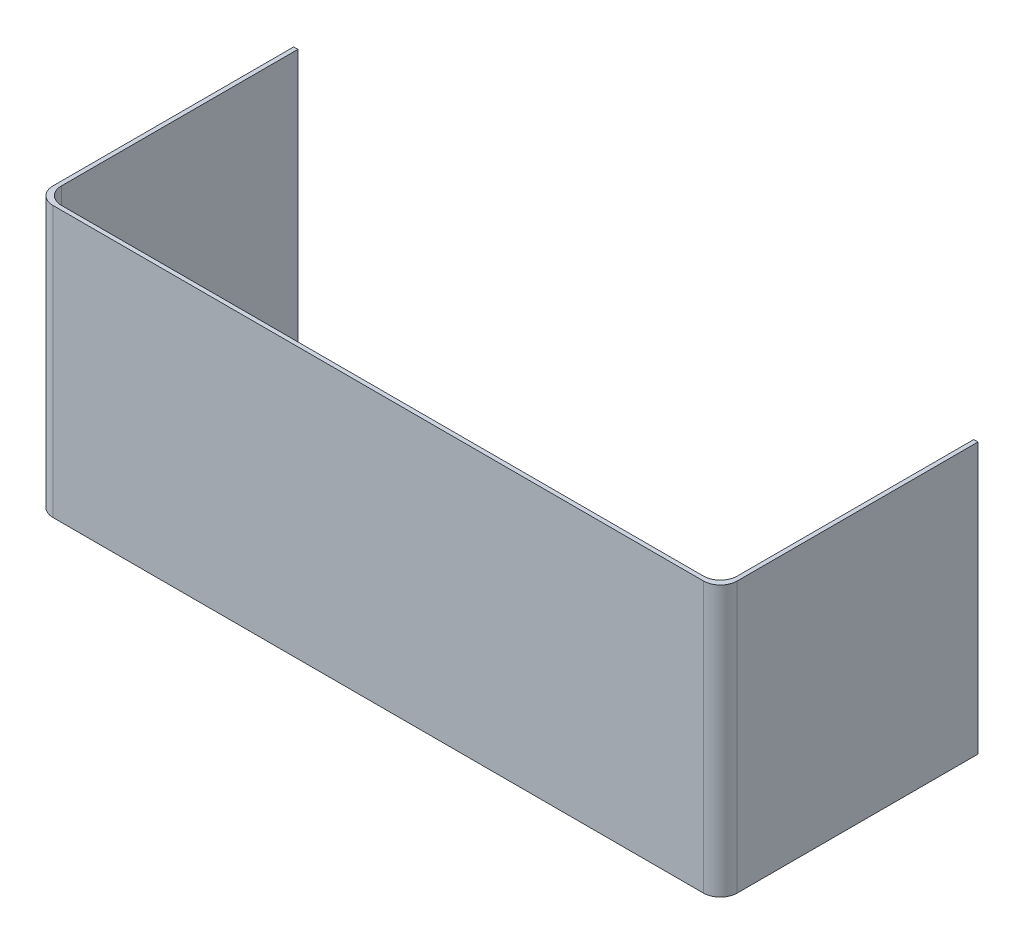
SolidWorks part; units mm, degrees
ref_plane "Front Plane" through (0, 0, 0) normal (0, 0, 1) x (1, 0, 0)
ref_plane "Top Plane" through (0, 0, 0) normal (0, 1, 0) x (1, 0, 0)
ref_plane "Right Plane" through (0, 0, 0) normal (1, 0, 0) x (0, 0, -1)
sketch "Sketch1" plane through (0, 0, 0) normal (0, 1, 0) x (1, 0, 0)
  line L0 (-64.2938, 47.625) -> (-63.5, 47.625)
  line L5 (-63.5, 47.625) -> (63.5, 47.625) construction
  line L6 (-63.5, 47.625) -> (-63.5, 0)
  line L7 (-63.5, 0) -> (63.5, 0)
  line L8 (63.5, 47.625) -> (63.5, 0)
  line L9 (-64.2938, 47.625) -> (64.2938, 47.625) construction
  line L10 (-64.2938, 47.625) -> (-64.2938, -0.7938)
  line L11 (-64.2938, -0.7938) -> (64.2938, -0.7938)
  line L12 (64.2938, 47.625) -> (64.2938, -0.7938)
  line L13 (64.2938, 47.625) -> (63.5, 47.625)
  point P4 (0, 47.625)
  point P5 (0, 0)
  dimension "D1" = 127
  dimension "D2" = 47.625
  dimension "D3" = 0.7937
  dimension "D4" = 0.7937
extrude "Boss-Extrude1" add sketch "Sketch1" along normal blind 50.8
fillet "Fillet1" radius 3.175 4 edges at (64.2938, 25.4, 0.7938) (-64.2938, 25.4, 0.7938) (63.5, 25.4, 0) (-63.5, 25.4, 0)
